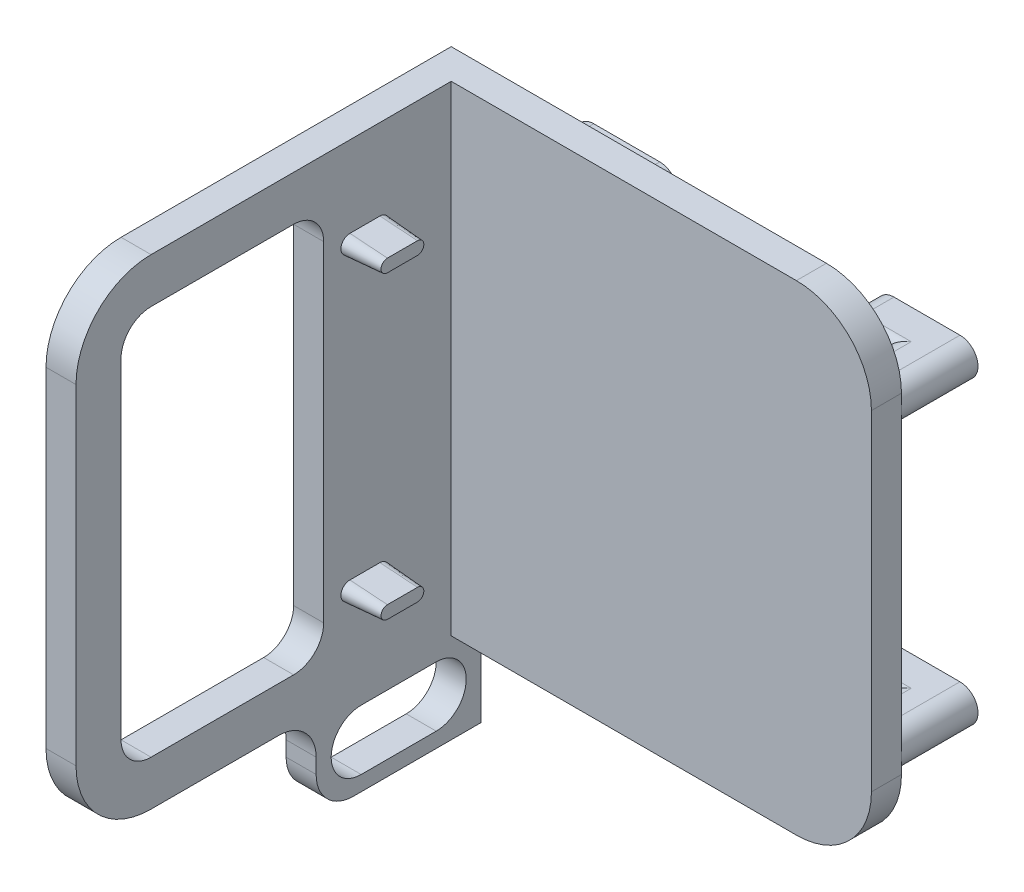
SolidWorks part; units mm, degrees
ref_plane "前视基准面" through (0, 0, 0) normal (0, 0, 1) x (1, 0, 0)
ref_plane "上视基准面" through (0, 0, 0) normal (0, 1, 0) x (1, 0, 0)
ref_plane "右视基准面" through (0, 0, 0) normal (1, 0, 0) x (0, 0, -1)
other "Configuration Table"
sketch "草图1" plane through (0, 0, 0) normal (0, 1, 0) x (1, 0, 0)
  line L1 (-118.5565, 30.4369) -> (-58.5565, 30.4369)
  line L2 (-118.5565, 30.4369) -> (-118.5565, 26.4369)
  line L3 (-118.5565, 26.4369) -> (-58.5565, 26.4369)
  line L4 (-58.5565, 30.4369) -> (-58.5565, 26.4369)
  dimension "D1" = 4
  dimension "D2" = 60
extrude "凸台-拉伸1" add sketch "草图1" along normal blind 64
sketch "草图2" plane through (0, 0, -26.4369) normal (0, 0, 1) x (1, 0, 0)
  line L0 (-118.5565, 0) -> (-58.5565, 0) construction
  line L1 (-118.5565, 64) -> (-114.5565, 64)
  line L2 (-118.5565, 64) -> (-118.5565, 0)
  line L3 (-118.5565, 0) -> (-114.5565, 0)
  line L4 (-114.5565, 64) -> (-114.5565, 0)
  dimension "D1" = 4
extrude "凸台-拉伸2" add sketch "草图2" along normal blind 50
fillet "圆角1" radius 10 4 edges at (-58.5565, 0, -28.4369) (-58.5565, 64, -28.4369) (-116.5565, 0, 23.5631) (-116.5565, 64, 23.5631)
sketch "草图3" plane through (-114.5565, 0, 0) normal (1, 0, 0) x (0, 0, -1)
  line L8 (-17.5631, 54) -> (-17.5631, 10)
  line L9 (-13.5631, 6) -> (20.4369, 6)
  line L10 (20.4369, 6) -> (20.4369, 58)
  line L11 (20.4369, 58) -> (-13.5631, 58)
  line L12 (-17.5631, 54) -> (-17.5631, 10)
  line L13 (-13.5631, 6) -> (20.4369, 6)
  line L14 (20.4369, 6) -> (20.4369, 58)
  line L15 (20.4369, 58) -> (-13.5631, 58)
  arc A4 (-17.5631, 10) -> (-13.5631, 6) centre (-13.5631, 10) ccw
  arc A5 (-13.5631, 58) -> (-17.5631, 54) centre (-13.5631, 54) ccw
  arc A6 (-17.5631, 10) -> (-13.5631, 6) centre (-13.5631, 10) ccw
  arc A7 (-13.5631, 58) -> (-17.5631, 54) centre (-13.5631, 54) ccw
  dimension "D1" = 6
extrude "切除-拉伸1" cut sketch "草图3" against normal up to next
sketch "草图4" plane through (-118.5565, 0, 0) normal (-1, 0, 0) x (0, 0, 1)
  line L0 (-20.4369, 6) -> (13.5631, 6) construction
  line L1 (-20.4369, 58) -> (-9.4369, 58)
  line L2 (-20.4369, 58) -> (-20.4369, 6)
  line L3 (-20.4369, 6) -> (-9.4369, 6)
  line L4 (-9.4369, 58) -> (-9.4369, 6)
  dimension "D1" = 11
extrude "凸台-拉伸3" add sketch "草图4" against normal blind 4 separate body
sketch "草图5" plane through (-114.5565, 0, 0) normal (1, 0, 0) x (0, 0, -1)
  line L0 (12.9369, 52) -> (16.9369, 52) construction
  line L1 (12.9369, 53.2) -> (16.9369, 53.2)
  line L2 (12.9369, 50.8) -> (16.9369, 50.8)
  line L3 (12.9369, 12) -> (16.9369, 12) construction
  line L4 (12.9369, 13.2) -> (16.9369, 13.2)
  line L5 (12.9369, 10.8) -> (16.9369, 10.8)
  arc A0 (12.9369, 53.2) -> (12.9369, 50.8) centre (12.9369, 52) ccw
  arc A1 (16.9369, 50.8) -> (16.9369, 53.2) centre (16.9369, 52) ccw
  arc A2 (12.9369, 13.2) -> (12.9369, 10.8) centre (12.9369, 12) ccw
  arc A3 (16.9369, 10.8) -> (16.9369, 13.2) centre (16.9369, 12) ccw
  point P4 (14.9369, 52)
  point P9 (14.9369, 12)
  dimension "D1" = 1.2
extrude "凸台-拉伸4" add sketch "草图5" along normal blind 5 draft 4
fillet "圆角2" radius 4 2 edges at (-116.5565, 58, -9.4369) (-116.5565, 6, -9.4369)
sketch "草图6" plane through (0, 0, -30.4369) normal (0, 0, -1) x (-1, 0, 0)
  line L0 (60.9565, 52) -> (63.4565, 52) construction
  line L1 (60.9565, 54.4) -> (63.4565, 54.4)
  line L2 (60.9565, 49.6) -> (63.4565, 49.6)
  line L3 (100.9565, 52) -> (103.4565, 52) construction
  line L4 (100.9565, 54.4) -> (103.4565, 54.4)
  line L5 (100.9565, 49.6) -> (103.4565, 49.6)
  line L6 (100.9565, 12) -> (103.4565, 12) construction
  line L7 (100.9565, 14.4) -> (103.4565, 14.4)
  line L8 (100.9565, 9.6) -> (103.4565, 9.6)
  line L9 (60.9565, 12) -> (63.4565, 12) construction
  line L10 (60.9565, 14.4) -> (63.4565, 14.4)
  line L11 (60.9565, 9.6) -> (63.4565, 9.6)
  line L12 (60.9565, 52) -> (60.9565, 12) construction
  line L13 (118.5565, 64) -> (118.5565, 0) construction
  line L14 (58.5565, 54) -> (58.5565, 10) construction
  arc A0 (60.9565, 54.4) -> (60.9565, 49.6) centre (60.9565, 52) ccw
  arc A1 (63.4565, 49.6) -> (63.4565, 54.4) centre (63.4565, 52) ccw
  arc A2 (100.9565, 54.4) -> (100.9565, 49.6) centre (100.9565, 52) ccw
  arc A3 (103.4565, 49.6) -> (103.4565, 54.4) centre (103.4565, 52) ccw
  arc A4 (100.9565, 14.4) -> (100.9565, 9.6) centre (100.9565, 12) ccw
  arc A5 (103.4565, 9.6) -> (103.4565, 14.4) centre (103.4565, 12) ccw
  arc A6 (60.9565, 14.4) -> (60.9565, 9.6) centre (60.9565, 12) ccw
  arc A7 (63.4565, 9.6) -> (63.4565, 14.4) centre (63.4565, 12) ccw
  point P2 (62.2065, 52)
  point P11 (102.2065, 52)
  point P18 (102.2065, 12)
  point P25 (62.2065, 12)
  point P32 (118.5565, 32)
  point P33 (60.9565, 32)
  point P36 (58.5565, 52)
  dimension "D1" = 2.4
  dimension "D2" = 2.5
  dimension "D3" = 2
  dimension "D4" = 2
extrude "凸台-拉伸5" add sketch "草图6" along normal blind 5.2
sketch "草图7" plane through (0, 0, -35.6369) normal (0, 0, -1) x (-1, 0, 0)
  line L0 (60.9565, 52) -> (69.7565, 52) construction
  line L1 (60.9565, 54.4) -> (69.7565, 54.4)
  line L2 (60.9565, 49.6) -> (69.7565, 49.6)
  line L3 (100.9565, 52) -> (109.7565, 52) construction
  line L4 (100.9565, 54.4) -> (109.7565, 54.4)
  line L5 (100.9565, 49.6) -> (109.7565, 49.6)
  line L6 (100.9565, 12) -> (109.7565, 12) construction
  line L7 (100.9565, 14.4) -> (109.7565, 14.4)
  line L8 (100.9565, 9.6) -> (109.7565, 9.6)
  line L9 (60.9565, 12) -> (69.7565, 12) construction
  line L10 (60.9565, 14.4) -> (69.7565, 14.4)
  line L11 (60.9565, 9.6) -> (69.7565, 9.6)
  arc A0 (60.9565, 54.4) -> (60.9565, 49.6) centre (60.9565, 52) ccw
  arc A1 (69.7565, 49.6) -> (69.7565, 54.4) centre (69.7565, 52) ccw
  arc A2 (60.9565, 54.4) -> (60.9565, 49.6) centre (60.9565, 52) ccw construction
  arc A3 (100.9565, 54.4) -> (100.9565, 49.6) centre (100.9565, 52) ccw
  arc A4 (109.7565, 49.6) -> (109.7565, 54.4) centre (109.7565, 52) ccw
  arc A5 (100.9565, 14.4) -> (100.9565, 9.6) centre (100.9565, 12) ccw
  arc A6 (109.7565, 9.6) -> (109.7565, 14.4) centre (109.7565, 12) ccw
  arc A7 (60.9565, 14.4) -> (60.9565, 9.6) centre (60.9565, 12) ccw
  arc A8 (69.7565, 9.6) -> (69.7565, 14.4) centre (69.7565, 12) ccw
  point P3 (65.3565, 52)
  point P15 (105.3565, 52)
  point P22 (105.3565, 12)
  point P29 (65.3565, 12)
  dimension "D1" = 8.8
  dimension "D2" = 2
  dimension "D3" = 2
extrude "凸台-拉伸6" add sketch "草图7" along normal blind 5
fillet "圆角3" radius 1 12 edges at (-66.6065, 49.6, -35.6369) (-66.6065, 54.4, -35.6369) (-66.6065, 9.6, -35.6369) (-66.6065, 14.4, -35.6369) (-106.6065, 9.6, -35.6369) (-106.6065, 14.4, -35.6369) (-106.6065, 49.6, -35.6369) (-106.6065, 54.4, -35.6369) (-72.1565, 52, -35.6369) (-72.1565, 12, -35.6369) (-112.1565, 12, -35.6369) (-112.1565, 52, -35.6369)
sketch "草图8" plane through (0, 0, 0) normal (0, -1, 0) x (1, 0, 0)
  line L0 (-114.5565, 13.5631) -> (-114.5565, -26.4369) construction
  line L1 (-118.5565, -30.4369) -> (-114.5565, -30.4369)
  line L2 (-118.5565, -30.4369) -> (-118.5565, -8.4369)
  line L3 (-118.5565, -8.4369) -> (-114.5565, -8.4369)
  line L4 (-114.5565, -30.4369) -> (-114.5565, -8.4369)
  dimension "D1" = 22
extrude "凸台-拉伸7" add sketch "草图8" along normal blind 12
fillet "圆角4" radius 5 2 edges at (-116.5565, 0, -8.4369) (-116.5565, -12, -8.4369)
sketch "草图9" plane through (-114.5565, 0, 0) normal (1, 0, 0) x (0, 0, -1)
  line L0 (14.4369, -6) -> (24.4369, -6) construction
  line L1 (14.4369, -2) -> (24.4369, -2)
  line L2 (14.4369, -10) -> (24.4369, -10)
  line L3 (30.4369, 0) -> (26.4369, 0) construction
  line L4 (30.4369, -12) -> (30.4369, 0) construction
  arc A0 (14.4369, -2) -> (14.4369, -10) centre (14.4369, -6) ccw
  arc A1 (24.4369, -10) -> (24.4369, -2) centre (24.4369, -6) ccw
  point P2 (19.4369, -6)
  dimension "D2" = 4
  dimension "D1" = 10
  dimension "D3" = 6
  dimension "D4" = 6
extrude "切除-拉伸2" cut sketch "草图9" against normal up to next
